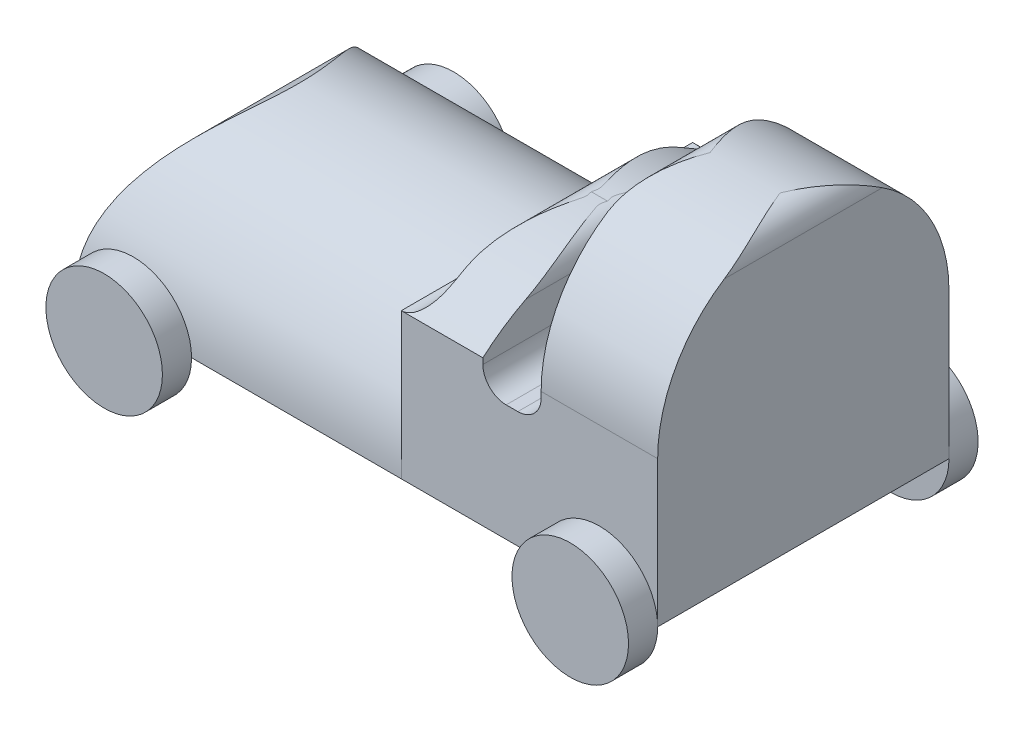
SolidWorks part; units mm, degrees
ref_plane "Front Plane" through (0, 0, 0) normal (0, 0, 1) x (1, 0, 0)
ref_plane "Top Plane" through (0, 0, 0) normal (0, 1, 0) x (1, 0, 0)
ref_plane "Right Plane" through (0, 0, 0) normal (1, 0, 0) x (0, 0, -1)
sketch "Sketch1" plane through (0, 0, 0) normal (0, 0, 1) x (1, 0, 0)
  line L1 (-25, 12.5) -> (25, 12.5)
  line L2 (-25, 12.5) -> (-25, -12.5)
  line L3 (-25, -12.5) -> (25, -12.5)
  line L4 (25, 12.5) -> (25, -12.5)
  line L5 (-25, 12.5) -> (25, -12.5) construction
  line L6 (-25, -12.5) -> (25, 12.5) construction
  point P1 (0, 0)
  dimension "D1" = 50
  dimension "D2" = 25
extrude "Boss-Extrude1" add sketch "Sketch1" along normal blind 25
sketch "Sketch2" plane through (0, 0, 25) normal (0, 0, 1) x (1, 0, 0)
  line L0 (-25, 0) -> (3, 0)
  line L1 (-25, 12.5) -> (-25, -12.5) construction
  line L2 (5, 2) -> (5, 2.5)
  line L3 (7, 4.5) -> (8, 4.5)
  line L4 (10, 2.5) -> (10, -0.5)
  line L5 (12, -2.5) -> (13, -2.5)
  line L6 (15, -0.5) -> (15, 10.5)
  line L7 (17, 12.5) -> (23, 12.5)
  line L8 (25, -12.5) -> (25, 12.5) construction
  line L9 (-25, -12.5) -> (25, -12.5) construction
  line L10 (25, 10.5) -> (25, -12.5)
  line L11 (25, -12.5) -> (-25, -12.5)
  line L12 (-25, 0) -> (-25, 12.5)
  line L13 (-25, 12.5) -> (25, 12.5)
  arc A0 (-25, -12.5) -> (-18.2916, 0) centre (-10, -12.5) cw
  arc A1 (3, 0) -> (5, 2) centre (3, 2) ccw
  arc A2 (15, 10.5) -> (17, 12.5) centre (17, 10.5) cw
  arc A3 (13, -2.5) -> (15, -0.5) centre (13, -0.5) ccw
  arc A4 (10, -0.5) -> (12, -2.5) centre (12, -0.5) ccw
  arc A5 (8, 4.5) -> (10, 2.5) centre (8, 2.5) cw
  arc A6 (5, 2.5) -> (7, 4.5) centre (7, 2.5) cw
  arc A7 (23, 12.5) -> (25, 10.5) centre (23, 10.5) cw
  point P22 (5, 0)
  point P27 (15, -2.5)
  point P30 (10, -2.5)
  point P33 (10, 4.5)
  point P36 (5, 4.5)
  point P40 (25, 12.5)
  dimension "D8" = 2
  dimension "D7" = 15
  dimension "D9" = 2
  dimension "D10" = 2
  dimension "D1" = 30
  dimension "D2" = 5
  dimension "D3" = 5
  dimension "D4" = 17
  dimension "D5" = 25
  dimension "D6" = 10
extrude "Cut-Extrude2" cut sketch "Sketch2" against normal blind 25
sketch "Sketch5" plane through (15, 0, 0) normal (-1, 0, 0) x (0, 0, 1)
  line L0 (0, 0) -> (25, 0)
  line L1 (0, 0) -> (0, 12.5)
  line L2 (0, 12.5) -> (25, 12.5)
  line L3 (25, 12.5) -> (25, 0)
  circle A0 centre (12.5, 0) radius 12.5
  line M1 (25, -0.5) -> (25, 10.5)
  line M2 (25, 10.5) -> (0, 10.5)
  line M3 (0, 10.5) -> (0, -0.5)
extrude "Cut-Extrude3" cut sketch "Sketch5" against normal through all both and the other way through all contours A0 L2 L1 M2 | A0 M2 M3 | A0 M1 M2 | A0 L3 L2 M2
sketch "Sketch7" plane through (0, 0, 0) normal (1, 0, 0) x (0, 0, -1)
  line L0 (0, 0) -> (-25, 0) construction
  line L1 (0, -12.5) -> (0, 0)
  line L2 (0, 0) -> (-25, 0)
  line L3 (-25, 0) -> (-25, -12.5)
  arc A0 (0, -12.5) -> (-25, -12.5) centre (-12.5, -12.5) ccw
extrude "Cut-Extrude5" cut sketch "Sketch7" against normal blind 28 and the other way blind 3 contours A0 L2 L3 | A0 L1 L2
sketch "Sketch8" plane through (3, 0, 0) normal (-1, 0, 0) x (0, 0, 1)
  line L0 (0, 0) -> (25, 0)
  line L1 (0, 0) -> (0, 4.4904)
  line L2 (25, 0) -> (25, 4.4904)
  line L3 (0, 4.4904) -> (25, 4.4904)
  line L4 (12.5, 4.4904) -> (12.5, 0)
  line L5 (12.5, 4.4904) -> (12.5, 6.6128)
  line L6 (12.5, 6.6128) -> (0, 6.6128)
  line L7 (0, 6.6128) -> (0, 4.4904)
  line L8 (12.5, 6.6128) -> (25, 6.6128)
  line L9 (25, 6.6128) -> (25, 4.4904)
  arc A0 (0, 0) -> (12.5, 4.4904) centre (11.9769, -13.6967) cw
  arc A1 (25, 0) -> (12.5, 4.4904) centre (13.0231, -13.6967) ccw
extrude "Cut-Extrude9" cut sketch "Sketch8" against normal blind 7 contours L3 A0 L5 L6 L7 | L1 A0 L3 | A1 L3 L9 L8 L5 | A1 L2 L3
sketch "Sketch9" plane through (0, 0, 25) normal (0, 0, 1) x (1, 0, 0)
  line L0 (-25, -12.5) -> (-20, -12.5)
  line L1 (3, -12.5) -> (25, -12.5) construction
  circle A0 centre (-20, -12.5) radius 5
  circle A1 centre (20, -12.5) radius 5
  dimension "D1" = 10
  dimension "D3" = 10
  dimension "D2" = 5
extrude "Boss-Extrude2" add sketch "Sketch9" along normal blind 2.5
sketch "Sketch10" plane through (0, 0, 0) normal (0, 0, -1) x (-1, 0, 0)
  line L0 (-15, -12.5) -> (-25, -12.5) construction
  circle A0 centre (-20, -12.5) radius 5
  circle A1 centre (20, -12.5) radius 5
extrude "Boss-Extrude3" add sketch "Sketch10" along normal blind 2.5
